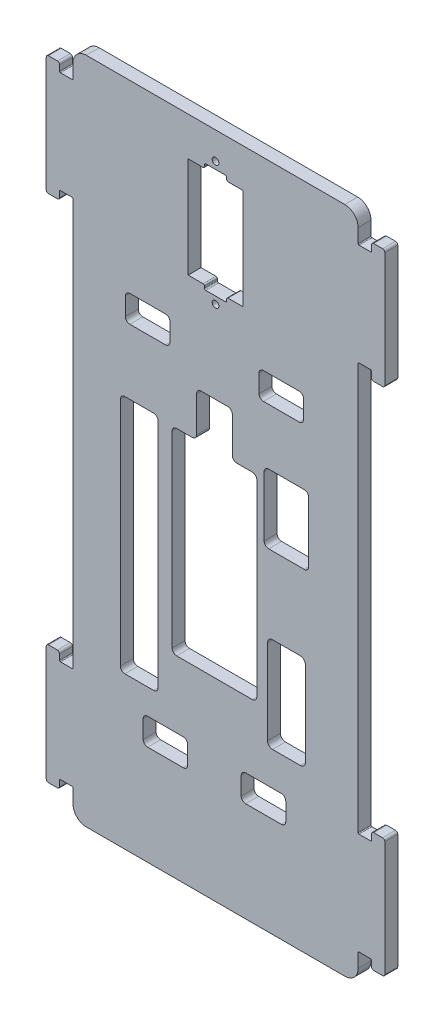
SolidWorks part; units mm, degrees
material "普通碳钢"
ref_plane "前视基准面" through (0, 0, 0) normal (0, 0, 1) x (1, 0, 0)
ref_plane "上视基准面" through (0, 0, 0) normal (0, 1, 0) x (1, 0, 0)
ref_plane "右视基准面" through (0, 0, 0) normal (1, 0, 0) x (0, 0, -1)
sketch "草图1" plane through (0, 0, 0) normal (0, 0, 1) x (1, 0, 0)
  line L0 (32.2, 68.7) -> (34.8, 68.7)
  line L1 (-29, 75) -> (29, 75)
  line L2 (-32, 72) -> (-32, -72) construction
  line L3 (-29, -75) -> (29, -75)
  line L4 (32, 72) -> (32, -72) construction
  line L5 (-32, 75) -> (32, -75) construction
  line L6 (-32, -75) -> (32, 75) construction
  line L7 (35, 68.9) -> (35, 70.15)
  line L8 (35.5, 70.65) -> (37.5, 70.65)
  line L9 (38, 70.15) -> (38, 44.35)
  line L10 (37.5, 43.85) -> (35.5, 43.85)
  line L11 (35, 44.35) -> (35, 45.6)
  line L12 (34.8, 45.8) -> (32.2, 45.8)
  line L13 (38, 57.25) -> (32, 57.25) construction
  line L14 (32, 68.9) -> (32, 72)
  line L15 (32, 45.6) -> (32, -45.6)
  line L16 (0, 0) -> (19.5271, 0) construction
  line L17 (0, 0) -> (0, 19.9471) construction
  line L18 (34.8, -45.8) -> (32.2, -45.8)
  line L19 (35, -44.35) -> (35, -45.6)
  line L20 (37.5, -43.85) -> (35.5, -43.85)
  line L21 (32, -68.9) -> (32, -72)
  line L22 (32.2, -68.7) -> (34.8, -68.7)
  line L23 (35, -68.9) -> (35, -70.15)
  line L24 (35.5, -70.65) -> (37.5, -70.65)
  line L25 (38, -70.15) -> (38, -44.35)
  line L26 (-37.5, 43.85) -> (-35.5, 43.85)
  line L27 (-35, 44.35) -> (-35, 45.6)
  line L28 (-34.8, 45.8) -> (-32.2, 45.8)
  line L29 (-32, 45.6) -> (-32, -45.6)
  line L30 (-34.8, -45.8) -> (-32.2, -45.8)
  line L31 (-35, -44.35) -> (-35, -45.6)
  line L32 (-37.5, -43.85) -> (-35.5, -43.85)
  line L33 (-38, -70.15) -> (-38, -44.35)
  line L34 (-35.5, -70.65) -> (-37.5, -70.65)
  line L35 (-35, -68.9) -> (-35, -70.15)
  line L36 (-32.2, -68.7) -> (-34.8, -68.7)
  line L37 (-32, -68.9) -> (-32, -72)
  line L38 (-37.5, 43.85) -> (-35.5, 43.85)
  line L39 (-32, 68.9) -> (-32, 72)
  line L40 (-32.2, 68.7) -> (-34.8, 68.7)
  line L41 (-35, 68.9) -> (-35, 70.15)
  line L42 (-35.5, 70.65) -> (-37.5, 70.65)
  line L43 (-38, 70.15) -> (-38, 44.35)
  arc A0 (-32, -72) -> (-29, -75) centre (-29, -72) ccw
  arc A1 (29, -75) -> (32, -72) centre (29, -72) ccw
  arc A2 (29, 75) -> (32, 72) centre (29, 72) cw
  arc A3 (-32, 72) -> (-29, 75) centre (-29, 72) cw
  arc A4 (35, 70.15) -> (35.5, 70.65) centre (35.5, 70.15) cw
  arc A5 (35, 44.35) -> (35.5, 43.85) centre (35.5, 44.35) ccw
  arc A6 (37.5, 43.85) -> (38, 44.35) centre (37.5, 44.35) ccw
  arc A7 (37.5, 70.65) -> (38, 70.15) centre (37.5, 70.15) cw
  arc A8 (37.5, 43.85) -> (38, 44.35) centre (37.5, 44.35) ccw
  arc A9 (34.8, 45.8) -> (35, 45.6) centre (34.8, 45.6) cw
  arc A10 (34.8, 68.7) -> (35, 68.9) centre (34.8, 68.9) ccw
  arc A11 (32, 45.6) -> (32.2, 45.8) centre (32.2, 45.6) cw
  arc A12 (32, 68.9) -> (32.2, 68.7) centre (32.2, 68.9) ccw
  arc A13 (32, -45.6) -> (32.2, -45.8) centre (32.2, -45.6) ccw
  arc A14 (34.8, -45.8) -> (35, -45.6) centre (34.8, -45.6) ccw
  arc A15 (35, -44.35) -> (35.5, -43.85) centre (35.5, -44.35) cw
  arc A16 (32, -68.9) -> (32.2, -68.7) centre (32.2, -68.9) cw
  arc A17 (34.8, -68.7) -> (35, -68.9) centre (34.8, -68.9) cw
  arc A18 (35, -70.15) -> (35.5, -70.65) centre (35.5, -70.15) ccw
  arc A19 (37.5, -70.65) -> (38, -70.15) centre (37.5, -70.15) ccw
  arc A20 (37.5, -43.85) -> (38, -44.35) centre (37.5, -44.35) cw
  arc A21 (-35, 44.35) -> (-35.5, 43.85) centre (-35.5, 44.35) cw
  arc A22 (-34.8, 45.8) -> (-35, 45.6) centre (-34.8, 45.6) ccw
  arc A23 (-32, 45.6) -> (-32.2, 45.8) centre (-32.2, 45.6) ccw
  arc A24 (-32, -45.6) -> (-32.2, -45.8) centre (-32.2, -45.6) cw
  arc A25 (-34.8, -45.8) -> (-35, -45.6) centre (-34.8, -45.6) cw
  arc A26 (-35, -44.35) -> (-35.5, -43.85) centre (-35.5, -44.35) ccw
  arc A27 (-37.5, -43.85) -> (-38, -44.35) centre (-37.5, -44.35) ccw
  arc A28 (-37.5, -70.65) -> (-38, -70.15) centre (-37.5, -70.15) cw
  arc A29 (-35, -70.15) -> (-35.5, -70.65) centre (-35.5, -70.15) cw
  arc A30 (-34.8, -68.7) -> (-35, -68.9) centre (-34.8, -68.9) ccw
  arc A31 (-32, -68.9) -> (-32.2, -68.7) centre (-32.2, -68.9) ccw
  arc A32 (-37.5, 43.85) -> (-38, 44.35) centre (-37.5, 44.35) cw
  arc A33 (-32, 68.9) -> (-32.2, 68.7) centre (-32.2, 68.9) cw
  arc A34 (-34.8, 68.7) -> (-35, 68.9) centre (-34.8, 68.9) cw
  arc A35 (-35, 70.15) -> (-35.5, 70.65) centre (-35.5, 70.15) ccw
  arc A36 (-37.5, 70.65) -> (-38, 70.15) centre (-37.5, 70.15) ccw
  point P0 (0, 0)
  point P33 (35, 69.525)
  point P45 (32, 45.8)
  point P53 (32, 68.7)
  point P75 (32, 0)
  point P77 (38, -57.25)
  dimension "D3" = 3
  dimension "D6" = 0.2
  dimension "D7" = 0.5
  dimension "D8" = 0.2
  dimension "D11" = 0.2
  dimension "D1" = 64
  dimension "D2" = 150
  dimension "D4" = 22.9
  dimension "D5" = 26.8
  dimension "D9" = 3
  dimension "D10" = 3
  dimension "D12" = 114.5
extrude "凸台-拉伸1" add sketch "草图1" along normal mid plane 2.9 contours L42 A36 L43 A32 L26 A21 L27 A22 L28 A23 L29 A24 L30 A25 L31 A26 L32 A27 L33 A28 L34 A29 L35 A30 L36 A31 L37 A0 L3 A1 L21 A16 L22 A17 L23 A18 L24 A19 L25 A20 L20 A15 L19 A14 L18 A13 L15 A11 L12 A9 L11
sketch "草图2" plane through (0, 0, 1.45) normal (0, 0, 1) x (1, 0, 0)
  line L0 (0, 0) -> (0, 55) construction
  line L1 (-6.15, 66.3) -> (6.15, 66.3)
  line L2 (-6.15, 66.3) -> (-6.15, 43.7)
  line L3 (-6.15, 43.7) -> (6.15, 43.7)
  line L4 (6.15, 66.3) -> (6.15, 43.7)
  line L5 (-6.15, 66.3) -> (6.15, 43.7) construction
  line L6 (-6.15, 43.7) -> (6.15, 66.3) construction
  line L7 (0, 55) -> (15.3315, 55) construction
  circle A0 centre (0, 41.1) radius 0.75
  circle A1 centre (0, 68.9) radius 0.75
  point P0 (0, 55)
  dimension "D3" = 1.5
  dimension "D1" = 22.6
  dimension "D2" = 12.3
  dimension "D4" = 27.8
  dimension "D5" = 55
extrude "切除-拉伸1" cut sketch "草图2" against normal through all
sketch "草图3" plane through (0, 0, 1.45) normal (0, 0, 1) x (1, 0, 0)
  line L0 (-2.5, 66.3) -> (-2.5, 67.3)
  line L1 (6.15, 66.3) -> (-6.15, 66.3) construction
  line L2 (-2.5, 67.3) -> (2.5, 67.3)
  line L3 (2.5, 67.3) -> (2.5, 66.3)
  line L4 (0, 66.3) -> (0, 63.4083) construction
  line L5 (-2.5, 66.3) -> (2.5, 66.3)
  line L6 (6.15, 55) -> (13.9493, 55) construction
  line L7 (6.15, 43.7) -> (6.15, 66.3) construction
  line L8 (-2.5, 43.7) -> (-2.5, 42.7)
  line L9 (-2.5, 42.7) -> (2.5, 42.7)
  line L10 (2.5, 42.7) -> (2.5, 43.7)
  line L11 (-2.5, 43.7) -> (2.5, 43.7)
  dimension "D1" = 1
  dimension "D2" = 5
extrude "切除-拉伸2" cut sketch "草图3" against normal through all
fillet "圆角1" radius 0.3 8 edges at (2.5, 43.7, 0) (2.5, 42.7, 0) (-2.5, 43.7, 0) (-2.5, 42.7, 0) (2.5, 66.3, 0) (2.5, 67.3, 0) (-2.5, 67.3, 0) (-2.5, 66.3, 0)
sketch "草图4" plane through (0, 0, 1.45) normal (0, 0, 1) x (1, 0, 0)
  line L0 (32, 45.6) -> (32, -45.6) construction
  line L1 (-20.36, 12.99) -> (-13.89, 12.99)
  line L2 (-21.36, 11.99) -> (-21.36, -39.9)
  line L3 (-20.36, -40.9) -> (-13.89, -40.9)
  line L4 (-12.89, 11.99) -> (-12.89, -39.9)
  line L5 (-21.36, 12.99) -> (-12.89, -40.9) construction
  line L6 (-21.36, -40.9) -> (-12.89, 12.99) construction
  line L7 (-8.74, 12.6) -> (8.26, 12.6)
  line L8 (-9.74, 11.6) -> (-9.74, -30.6)
  line L9 (-8.74, -31.6) -> (8.26, -31.6)
  line L10 (9.26, 11.6) -> (9.26, -30.6)
  line L11 (-9.74, 12.6) -> (9.26, -31.6) construction
  line L12 (-9.74, -31.6) -> (9.26, 12.6) construction
  line L13 (11.91, 15.03) -> (19.91, 15.03)
  line L14 (10.91, 14.03) -> (10.91, 0.53)
  line L15 (11.91, -0.47) -> (19.91, -0.47)
  line L16 (20.91, 14.03) -> (20.91, 0.53)
  line L17 (10.91, 15.03) -> (20.91, -0.47) construction
  line L18 (10.91, -0.47) -> (20.91, 15.03) construction
  line L19 (12.8018, -17.71) -> (19.0282, -17.71)
  line L20 (11.68, -18.8318) -> (11.68, -37.9082)
  line L21 (12.8018, -39.03) -> (19.0282, -39.03)
  line L22 (20.15, -18.8318) -> (20.15, -37.9082)
  line L23 (11.68, -17.71) -> (20.15, -39.03) construction
  line L24 (11.68, -39.03) -> (20.15, -17.71) construction
  line L25 (-29, -75) -> (29, -75) construction
  line L26 (-32, 45.6) -> (-32, -45.6) construction
  arc A0 (-21.36, -39.9) -> (-20.36, -40.9) centre (-20.36, -39.9) ccw
  arc A1 (-13.89, -40.9) -> (-12.89, -39.9) centre (-13.89, -39.9) ccw
  arc A2 (-12.89, 11.99) -> (-13.89, 12.99) centre (-13.89, 11.99) ccw
  arc A3 (-20.36, 12.99) -> (-21.36, 11.99) centre (-20.36, 11.99) ccw
  arc A4 (-8.74, 12.6) -> (-9.74, 11.6) centre (-8.74, 11.6) ccw
  arc A5 (-9.74, -30.6) -> (-8.74, -31.6) centre (-8.74, -30.6) ccw
  arc A6 (8.26, -31.6) -> (9.26, -30.6) centre (8.26, -30.6) ccw
  arc A7 (9.26, 11.6) -> (8.26, 12.6) centre (8.26, 11.6) ccw
  arc A8 (19.91, 15.03) -> (20.91, 14.03) centre (19.91, 14.03) cw
  arc A9 (20.91, 0.53) -> (19.91, -0.47) centre (19.91, 0.53) cw
  arc A10 (11.91, -0.47) -> (10.91, 0.53) centre (11.91, 0.53) cw
  arc A11 (10.91, 14.03) -> (11.91, 15.03) centre (11.91, 14.03) cw
  arc A12 (11.68, -37.9082) -> (12.8018, -39.03) centre (12.8018, -37.9082) ccw
  arc A13 (19.0282, -39.03) -> (20.15, -37.9082) centre (19.0282, -37.9082) ccw
  arc A14 (20.15, -18.8318) -> (19.0282, -17.71) centre (19.0282, -18.8318) ccw
  arc A15 (11.68, -18.8318) -> (12.8018, -17.71) centre (12.8018, -18.8318) cw
  point P0 (-17.125, -13.955)
  point P17 (-0.24, -9.5)
  point P22 (15.91, 7.28)
  point P27 (15.915, -28.37)
  dimension "D3" = 1
  dimension "D8" = 1
  dimension "D13" = 1
  dimension "D18" = 1.1218
  dimension "D1" = 53.89
  dimension "D2" = 8.47
  dimension "D4" = 10.64
  dimension "D5" = 34.1
  dimension "D6" = 19
  dimension "D7" = 44.2
  dimension "D9" = 43.4
  dimension "D10" = 22.26
  dimension "D11" = 15.5
  dimension "D12" = 10
  dimension "D14" = 11.09
  dimension "D15" = 74.53
  dimension "D16" = 21.32
  dimension "D17" = 8.47
  dimension "D19" = 11.85
  dimension "D20" = 35.97
extrude "切除-拉伸3" cut sketch "草图4" against normal through all
sketch "草图5" plane through (0, 0, 1.45) normal (0, 0, 1) x (1, 0, 0)
  line L0 (-0.24, 12.6) -> (-0.24, 22.6) construction
  line L1 (8.26, 12.6) -> (-8.74, 12.6) construction
  line L3 (-3.24, 22.6) -> (2.76, 22.6)
  line L4 (3.76, 21.6) -> (3.76, 12.6)
  line L5 (-4.24, 21.6) -> (-4.24, 12.6)
  line L6 (3.76, 12.6) -> (-4.24, 12.6)
  arc A0 (3.76, 21.6) -> (2.76, 22.6) centre (2.76, 21.6) ccw
  arc A1 (-3.24, 22.6) -> (-4.24, 21.6) centre (-3.24, 21.6) ccw
  point P11 (3.76, 22.6)
  point P14 (-4.24, 22.6)
  dimension "D3" = 1
  dimension "D1" = 10
  dimension "D2" = 8
extrude "切除-拉伸4" cut sketch "草图5" against normal through all
fillet "圆角2" radius 1 2 edges at (3.76, 12.6, 0) (-4.24, 12.6, 0)
sketch "草图6" plane through (0, 0, 1.45) normal (0, 0, 1) x (1, 0, 0)
  line L0 (-0.24, 22.6) -> (-0.24, 29.3114) construction
  line L1 (10.76, 33.6) -> (18.76, 33.6)
  line L2 (9.76, 32.6) -> (9.76, 28.6)
  line L3 (10.76, 27.6) -> (18.76, 27.6)
  line L4 (19.76, 32.6) -> (19.76, 28.6)
  line L5 (9.76, 33.6) -> (19.76, 27.6) construction
  line L6 (9.76, 27.6) -> (19.76, 33.6) construction
  line L7 (2.76, 22.6) -> (-3.24, 22.6) construction
  line L8 (8.26, 12.6) -> (4.76, 12.6) construction
  line L9 (-8.74, -31.6) -> (8.26, -31.6) construction
  line L10 (6.76, -46.6) -> (14.76, -46.6)
  line L11 (5.76, -47.6) -> (5.76, -51.6)
  line L12 (6.76, -52.6) -> (14.76, -52.6)
  line L13 (15.76, -47.6) -> (15.76, -51.6)
  line L14 (5.76, -46.6) -> (15.76, -52.6) construction
  line L15 (5.76, -52.6) -> (15.76, -46.6) construction
  line L16 (-10.24, 32.6) -> (-10.24, 28.6)
  line L17 (-11.24, 33.6) -> (-19.24, 33.6)
  line L18 (-20.24, 32.6) -> (-20.24, 28.6)
  line L19 (-11.24, 27.6) -> (-19.24, 27.6)
  line L20 (-6.24, -47.6) -> (-6.24, -51.6)
  line L21 (-7.24, -46.6) -> (-15.24, -46.6)
  line L22 (-16.24, -47.6) -> (-16.24, -51.6)
  line L23 (-7.24, -52.6) -> (-15.24, -52.6)
  arc A0 (10.76, 33.6) -> (9.76, 32.6) centre (10.76, 32.6) ccw
  arc A1 (9.76, 28.6) -> (10.76, 27.6) centre (10.76, 28.6) ccw
  arc A2 (18.76, 27.6) -> (19.76, 28.6) centre (18.76, 28.6) ccw
  arc A3 (19.76, 32.6) -> (18.76, 33.6) centre (18.76, 32.6) ccw
  arc A4 (15.76, -51.6) -> (14.76, -52.6) centre (14.76, -51.6) cw
  arc A5 (6.76, -52.6) -> (5.76, -51.6) centre (6.76, -51.6) cw
  arc A6 (5.76, -47.6) -> (6.76, -46.6) centre (6.76, -47.6) cw
  arc A7 (14.76, -46.6) -> (15.76, -47.6) centre (14.76, -47.6) cw
  arc A8 (-10.24, 28.6) -> (-11.24, 27.6) centre (-11.24, 28.6) cw
  arc A9 (-11.24, 33.6) -> (-10.24, 32.6) centre (-11.24, 32.6) cw
  arc A10 (-20.24, 32.6) -> (-19.24, 33.6) centre (-19.24, 32.6) cw
  arc A11 (-19.24, 27.6) -> (-20.24, 28.6) centre (-19.24, 28.6) cw
  arc A12 (-7.24, -52.6) -> (-6.24, -51.6) centre (-7.24, -51.6) ccw
  arc A13 (-6.24, -47.6) -> (-7.24, -46.6) centre (-7.24, -47.6) ccw
  arc A14 (-15.24, -46.6) -> (-16.24, -47.6) centre (-15.24, -47.6) ccw
  arc A15 (-16.24, -51.6) -> (-15.24, -52.6) centre (-15.24, -51.6) ccw
  point P0 (14.76, 30.6)
  point P23 (10.76, -49.6)
  point P28 (10.76, -52.6)
  point P41 (10.76, -46.6)
  point P68 (-6.24, -49.6)
  point P69 (5.76, -49.6)
  dimension "D3" = 1
  dimension "D7" = 1
  dimension "D1" = 10
  dimension "D2" = 6
  dimension "D4" = 15
  dimension "D5" = 10
  dimension "D6" = 6
  dimension "D8" = 15
  dimension "D9" = 20
  dimension "D10" = 12
extrude "切除-拉伸5" cut sketch "草图6" against normal through all
